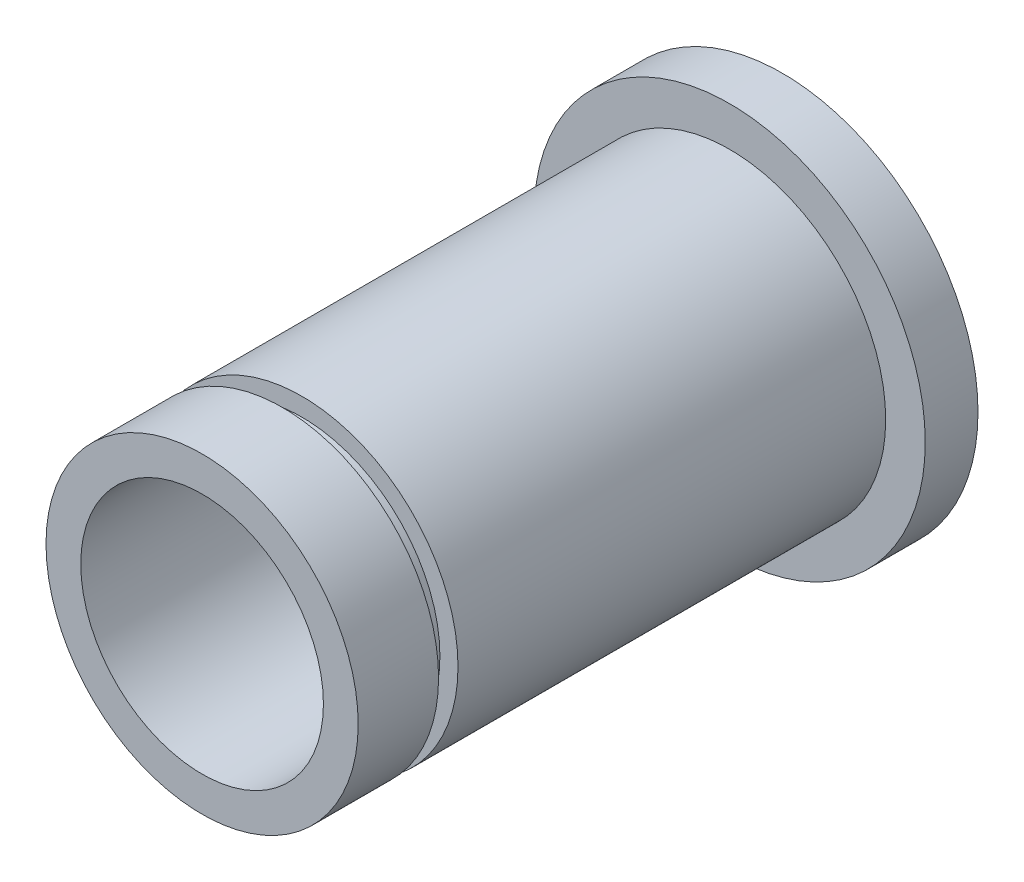
SolidWorks part; units mm, degrees
material "6061-T6 (SS)"
ref_plane "Front Plane" through (0, 0, 0) normal (0, 0, 1) x (1, 0, 0)
ref_plane "Top Plane" through (0, 0, 0) normal (0, 1, 0) x (1, 0, 0)
ref_plane "Right Plane" through (0, 0, 0) normal (1, 0, 0) x (0, 0, -1)
sketch "Sketch1" plane through (0, 0, 0) normal (1, 0, 0) x (0, 0, -1)
  line L0 (0, 5.9182) -> (3.048, 5.9182)
  line L1 (0, 4.6) -> (0, 5.9182)
  line L8 (0, 0) -> (15.3934, 0) construction
  line L9 (0, 0) -> (0, -9.0032) construction
  line L12 (3.7846, 5.9182) -> (20, 5.9182)
  line L13 (3.048, 5.2324) -> (3.048, 5.9182)
  line L14 (3.7846, 5.2324) -> (3.048, 5.2324)
  line L15 (3.7846, 5.9182) -> (3.7846, 5.2324)
  line L16 (22, 7.4182) -> (22, 4.6)
  line L17 (20, 7.4182) -> (22, 7.4182)
  line L18 (20, 5.9182) -> (20, 7.4182)
  line L19 (0, 4.6) -> (22, 4.6)
  dimension "D1" = 11.8364
  dimension "D2" = 3.048
  dimension "D3" = 9.2
  dimension "D4" = 0.7366
  dimension "D5" = 1.5
  dimension "D6" = 2
  dimension "D7" = 20
  dimension "D9" = 10.4648
revolve "Revolve1" add sketch "Sketch1" angle 360 about L8
